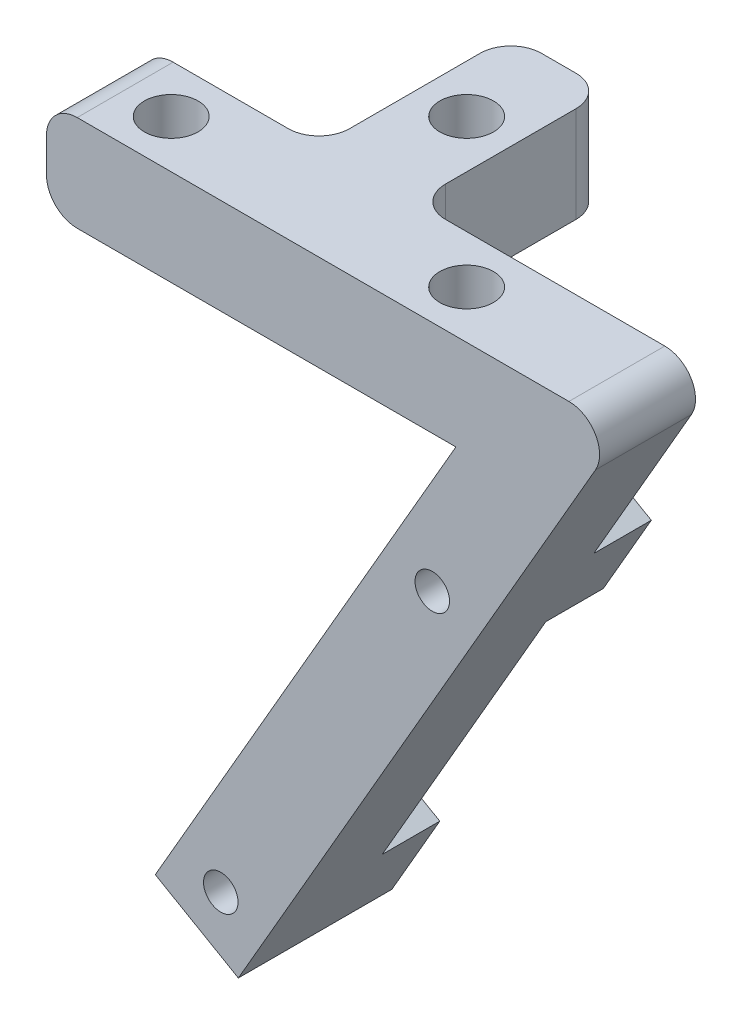
SolidWorks part; units mm, degrees
material "Copper"
ref_plane "Front Plane" through (0, 0, 0) normal (0, 0, 1) x (1, 0, 0)
ref_plane "Top Plane" through (0, 0, 0) normal (0, 1, 0) x (1, 0, 0)
ref_plane "Right Plane" through (0, 0, 0) normal (1, 0, 0) x (0, 0, -1)
sketch "Sketch2" plane through (0, 0, 0) normal (0, 0, 1) x (1, 0, 0)
  line L0 (0, 0) -> (38.1, 0)
  line L5 (38.1, 0) -> (12.7, -43.9941)
  line L6 (12.7, -43.9941) -> (7.2007, -40.8191)
  line L7 (7.2007, -40.8191) -> (27.1015, -6.35)
  line L8 (27.1015, -6.35) -> (0, -6.35)
  line L9 (0, -6.35) -> (0, 0)
  dimension "D1" = 6.35
  dimension "D2" = 6.35
  dimension "D3" = 60
  dimension "D4" = 50.8
  dimension "D5" = 38.1
extrude "Boss-Extrude2" add sketch "Sketch2" along normal blind 6.35
sketch "Sketch5" plane through (0, 0, 0) normal (0, 1, 0) x (1, 0, 0)
  line L0 (38.1, -6.35) -> (0, -6.35) construction
  line L1 (0, -6.35) -> (0, 0) construction
  circle A0 centre (5.08, -3.175) radius 1.778
  circle A1 centre (24.638, -3.175) radius 1.778
  dimension "D1" = 3.556
  dimension "D2" = 3.556
  dimension "D4" = 3.175
  dimension "D3" = 3.175
  dimension "D5" = 19.558
  dimension "D6" = 5.08
extrude "Cut-Extrude1" cut sketch "Sketch5" against normal blind 6.35
sketch "Sketch7" plane through (0, 0, 0) normal (0, 1, 0) x (1, 0, 0)
  line L0 (38.1, 0) -> (0, 0) construction
  line L1 (11.684, 0) -> (18.034, 0)
  line L2 (11.684, 0) -> (11.684, 12.7)
  line L3 (11.684, 12.7) -> (18.034, 12.7)
  line L4 (18.034, 0) -> (18.034, 12.7)
  circle A0 centre (5.08, -3.175) radius 1.778 construction
  point P6 (14.859, 0)
  dimension "D1" = 12.7
  dimension "D2" = 6.35
  dimension "D3" = 9.779
extrude "Boss-Extrude3" add sketch "Sketch7" against normal blind 6.35
sketch "Sketch8" plane through (0, 0, 0) normal (0, 1, 0) x (1, 0, 0)
  circle A0 centre (14.859, 6.604) radius 1.778
  circle A1 centre (5.08, -3.175) radius 1.778 construction
  dimension "D1" = 3.556
  dimension "D2" = 9.779
  dimension "D3" = 9.779
extrude "Cut-Extrude3" cut sketch "Sketch8" against normal blind 6.35
sketch "Sketch9" plane through (0, 0, 6.35) normal (0, 0, 1) x (1, 0, 0)
  line L0 (12.7, -43.9941) -> (38.1, 0) construction
  line L1 (7.2007, -40.8191) -> (12.7, -43.9941) construction
  circle A0 centre (11.5379, -39.657) radius 1.143
  circle A1 centre (25.5378, -15.4083) radius 1.143
  point P8 (0, 0)
  dimension "D1" = 27.9999
  dimension "D2" = 2.286
  dimension "D3" = 2.286
  dimension "D4" = 3.175
  dimension "D5" = 3.175
  dimension "D6" = 3.175
extrude "Cut-Extrude4" cut sketch "Sketch9" against normal blind 12.7
sketch "Sketch11" plane through (0, 0, 0) normal (0, 0, -1) x (-1, 0, 0)
  line L0 (-29.875, -14.2462) -> (-24.3757, -11.0712)
  line L1 (-12.7, -43.9941) -> (-38.1, 0) construction
  line L2 (-27.1015, -6.35) -> (-7.2007, -40.8191) construction
  line L3 (-24.3757, -11.0712) -> (-21.2007, -16.5704)
  line L4 (-21.2007, -16.5704) -> (-26.7, -19.7454)
  line L5 (-26.7, -19.7454) -> (-29.875, -14.2462)
  line L6 (-15.875, -38.4948) -> (-10.3757, -35.3198)
  line L7 (-10.3757, -35.3198) -> (-7.2007, -40.8191)
  line L8 (-7.2007, -40.8191) -> (-12.7, -43.9941)
  line L9 (-12.7, -43.9941) -> (-15.875, -38.4948)
  circle A0 centre (-25.5378, -15.4083) radius 1.143 construction
  dimension "D1" = 6.35
  dimension "D2" = 3.175
  dimension "D3" = 6.35
extrude "Boss-Extrude5" add sketch "Sketch11" along normal blind 3.81
fillet "Fillet1" radius 2.032 7 edges at (11.684, -3.175, -12.7) (18.034, -3.175, -12.7) (18.034, -3.175, 0) (11.684, -3.175, 0) (0, 0, 3.175) (0, -6.35, 3.175) (38.1, 0, 3.175)
sketch "Sketch12" plane through (0, 0, 6.35) normal (0, 0, 1) x (1, 0, 0)
  circle A0 centre (25.5378, -15.4083) radius 1.143
  circle A1 centre (11.5379, -39.657) radius 1.143
extrude "Cut-Extrude5" cut sketch "Sketch12" against normal blind 12.7
